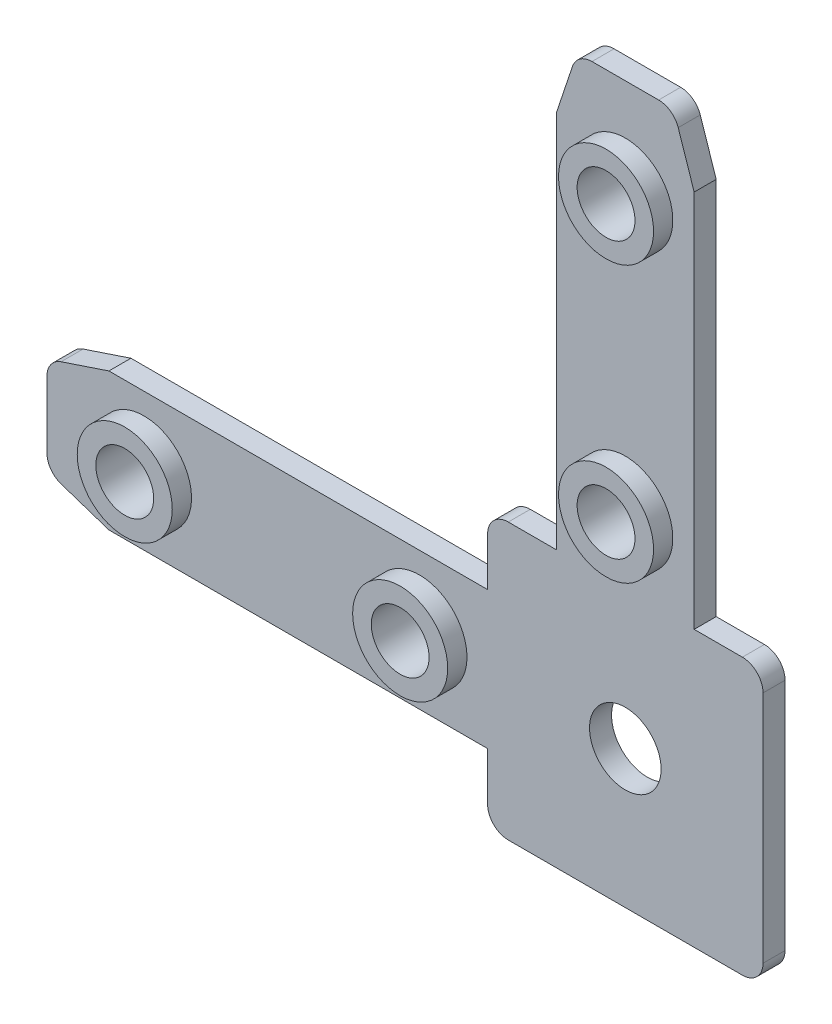
SolidWorks part; units mm, degrees
material "Plain Carbon Steel"
ref_plane "Front Plane" through (0, 0, 0) normal (0, 0, 1) x (1, 0, 0)
ref_plane "Top Plane" through (0, 0, 0) normal (0, 1, 0) x (1, 0, 0)
ref_plane "Right Plane" through (0, 0, 0) normal (1, 0, 0) x (0, 0, -1)
sketch "Sketch1" plane through (0, 0, 0) normal (0, 0, 1) x (1, 0, 0)
  line L0 (-10, 0) -> (0, 0) construction
  line L1 (0, 0) -> (0, 42) construction
  line L2 (-10, -8.5) -> (-10, -5)
  line L3 (-8.5, 10) -> (-5, 10)
  line L4 (-5, 10) -> (-5, 37.5)
  line L5 (-5, 37.5) -> (-3.8419, 40.9743)
  line L6 (-2.4189, 42) -> (2.4189, 42)
  line L7 (5, 37.5) -> (3.8419, 40.9743)
  line L8 (5, 10) -> (5, 37.5)
  line L9 (8.5, 10) -> (5, 10)
  line L10 (10, -8.5) -> (10, 8.5)
  line L11 (8.5, -10) -> (5, -10)
  line L12 (-5, -10) -> (5, -10)
  line L17 (-8.5, -10) -> (-5, -10)
  line L18 (-10, 5) -> (-37.5, 5)
  line L19 (-37.5, 5) -> (-40.9743, 3.8419)
  line L20 (-42, 2.4189) -> (-42, -2.4189)
  line L21 (-37.5, -5) -> (-40.9743, -3.8419)
  line L22 (-10, -5) -> (-37.5, -5)
  line L23 (-10, 5) -> (-10, 8.5)
  circle A0 centre (0, 0) radius 2.6
  arc A3 (-3.8419, 40.9743) -> (-2.4189, 42) centre (-2.4189, 40.5) cw
  arc A4 (3.8419, 40.9743) -> (2.4189, 42) centre (2.4189, 40.5) ccw
  arc A5 (-8.5, -10) -> (-10, -8.5) centre (-8.5, -8.5) cw
  arc A6 (-10, 8.5) -> (-8.5, 10) centre (-8.5, 8.5) cw
  arc A7 (8.5, 10) -> (10, 8.5) centre (8.5, 8.5) cw
  arc A8 (8.5, -10) -> (10, -8.5) centre (8.5, -8.5) ccw
  arc A9 (-40.9743, -3.8419) -> (-42, -2.4189) centre (-40.5, -2.4189) cw
  arc A10 (-40.9743, 3.8419) -> (-42, 2.4189) centre (-40.5, 2.4189) ccw
  point P15 (10, 0)
  point P30 (-3.5, 42)
  point P33 (3.5, 42)
  point P36 (-10, -10)
  point P39 (-10, 10)
  point P42 (10, 10)
  point P45 (10, -10)
  point P51 (-42, 0)
  point P55 (-42, -3.5)
  point P58 (-42, 3.5)
  dimension "D4" = 5.2
  dimension "D8" = 1.5
  dimension "D9" = 10
  dimension "D10" = 32
  dimension "D11" = 4.5
  dimension "D13" = 1.5
  dimension "D1" = 20
  dimension "D2" = 20
  dimension "D3" = 10
  dimension "D5" = 4.5
  dimension "D6" = 32
  dimension "D7" = 7
  dimension "D12" = 7
extrude "Boss-Extrude1" add sketch "Sketch1" along normal blind 1.6
sketch "Sketch2" plane through (0, 0, 1.6) normal (0, 0, 1) x (1, 0, 0)
  line L0 (-42, 0) -> (0, 0) construction
  line L2 (0, 0) -> (0, 42) construction
  line L3 (2.4189, 42) -> (-2.4189, 42) construction
  line L4 (-42, 2.4189) -> (-42, -2.4189) construction
  circle A0 centre (0, 14.95) radius 3.45
  circle A1 centre (0, 34.95) radius 3.45
  circle A4 centre (-14.95, 0) radius 3.45
  circle A5 centre (-34.95, 0) radius 3.45
  circle A6 centre (0, 0) radius 2.6 construction
  dimension "D1" = 6.9
  dimension "D3" = 14.95
  dimension "D5" = 14.95
  dimension "D2" = 20
  dimension "D4" = 20
extrude "Boss-Extrude2" add sketch "Sketch2" along normal blind 1.4
hole_wizard "M5x0.8 Tapped Hole1" positions "Sketch4" profile "Sketch3" tap size "M5x0.8" standard "ANSI Metric" end condition through all
sketch "Sketch4" plane through (0, 0, 3) normal (0, 0, 1) x (1, 0, 0)
  point P0 (0, 34.95)
  point P3 (0, 14.95)
  point P13 (-14.95, 0)
  point P16 (-34.95, 0)
cosmetic thread "Hole Thread3" parameters "D2"=5
cosmetic thread "Hole Thread4" parameters "D2"=5
cosmetic thread "Hole Thread5" parameters "D2"=5
cosmetic thread "Hole Thread6" parameters "D2"=5
sketch "Sketch3" plane through (0, 34.95, 3) normal (1, 0, 0) x (0, -1, 0)
  line L0 (0, 0) -> (0, 3)
  line L1 (0, 3) -> (2.1, 3)
  line L2 (2.1, 3) -> (2.1, 0)
  line L5 (2.1, 0) -> (0, 0)
  line L11 (0, -6.35) -> (0, 107.95) construction
  dimension "Thru Tap Drill Dia." = 4.2
  dimension "Thru Tap Drill Depth" = 3
